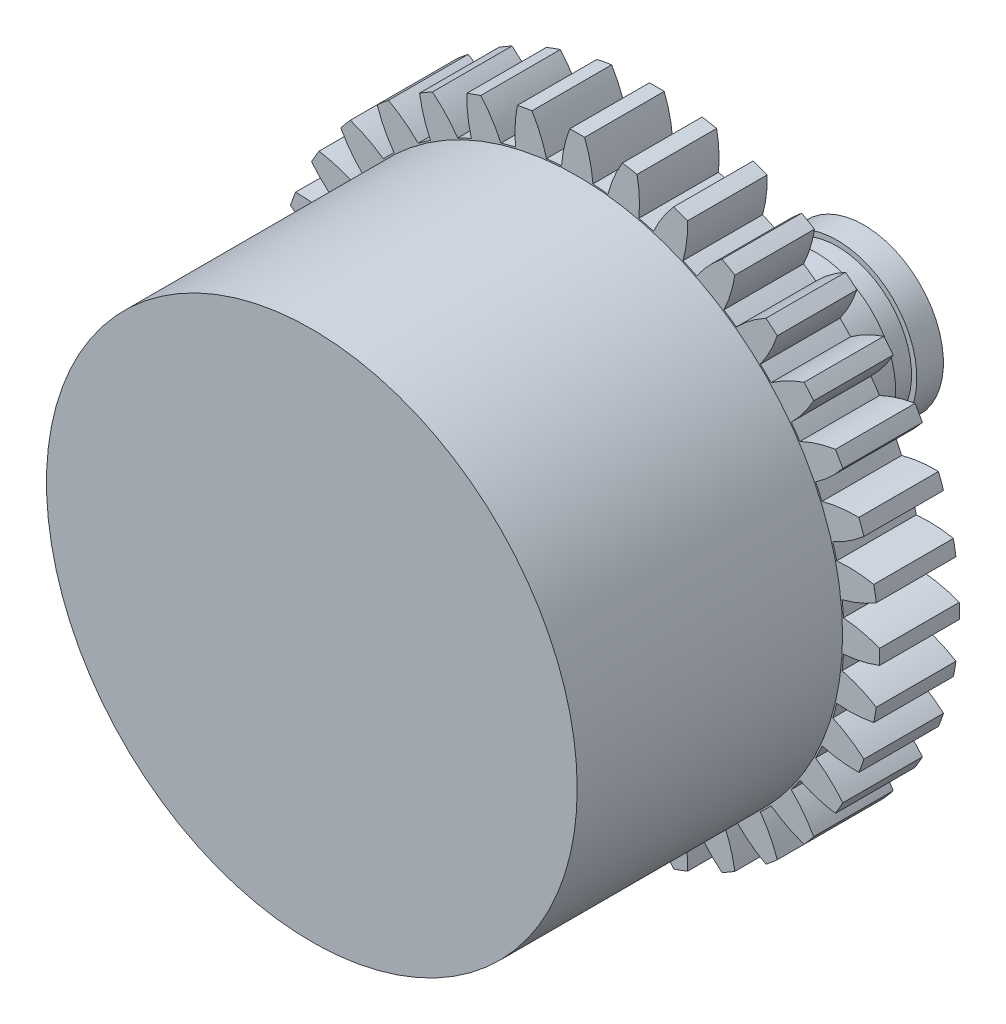
SolidWorks part; units mm, degrees
ref_plane "정면" through (0, 0, 0) normal (0, 0, 1) x (1, 0, 0)
ref_plane "윗면" through (0, 0, 0) normal (0, 1, 0) x (1, 0, 0)
ref_plane "우측면" through (0, 0, 0) normal (1, 0, 0) x (0, 0, -1)
sketch "스케치1" plane through (0, 0, 0) normal (0, 0, 1) x (1, 0, 0)
  circle A0 centre (0, 0) radius 5
  dimension "D1" = 10
extrude "보스-돌출1" add sketch "스케치1" along normal blind 5
sketch "스케치2" plane through (0, 0, 0) normal (0, 0, -1) x (-1, 0, 0)
  circle A0 centre (0, 0) radius 1.5
  dimension "D1" = 3
extrude "보스-돌출2" add sketch "스케치2" along normal blind 5.4
sketch "스케치3" plane through (0, 0, 0) normal (0, 0, -1) x (-1, 0, 0)
  circle A0 centre (0, 0) radius 2
  dimension "D1" = 4
extrude "보스-돌출3" add sketch "스케치3" along normal blind 2
sketch "스케치4" plane through (0, 0, -5.4) normal (0, 0, -1) x (-1, 0, 0)
  circle A0 centre (0, 0) radius 0.79
  dimension "D1" = 1.58
extrude "컷-돌출1" cut sketch "스케치4" against normal blind 1.5
sketch "스케치5" plane through (0, 0, 0) normal (0, 0, -1) x (-1, 0, 0)
  line L0 (0, 0) -> (0, 5.7) construction
  line L1 (0, 0) -> (-0.2355, 5.3949) construction
  line L2 (-0.2355, 5.3949) -> (-0.1399, 5.6983) construction
  line L3 (-0.2355, 5.3949) -> (-1.0666, 0.1696) construction
  circle A0 centre (0, 0) radius 5.4 construction
  circle A1 centre (0, 0) radius 5.7 construction
  circle A2 centre (0, 0) radius 5.025 construction
  circle A3 centre (0, 0) radius 1.08 construction
  arc A4 (-0.2958, 5.0163) -> (-0.1399, 5.6983) centre (2.074, 4.8335) cw
  arc A5 (0.2958, 5.0163) -> (0.1399, 5.6983) centre (-2.074, 4.8335) ccw
  arc A6 (-0.1399, 5.6983) -> (0.1399, 5.6983) centre (0, 0) cw
  arc A7 (1.1623, 4.8887) -> (1.1272, 5.5874) centre (-1.2031, 5.1202) ccw
  arc A8 (0.8517, 5.636) -> (1.1272, 5.5874) centre (0, 0) cw
  arc A9 (0.5798, 4.9914) -> (0.8517, 5.636) centre (2.8818, 4.3999) cw
  arc A10 (1.9936, 4.6126) -> (2.0804, 5.3068) centre (-0.2957, 5.2513) ccw
  arc A11 (1.8175, 5.4025) -> (2.0804, 5.3068) centre (0, 0) cw
  arc A12 (1.4378, 4.8149) -> (1.8175, 5.4025) centre (3.602, 3.8326) cw
  arc A13 (2.7643, 4.1964) -> (2.9703, 4.8649) centre (0.6206, 5.2229) ccw
  arc A14 (2.728, 5.0048) -> (2.9703, 4.8649) centre (0, 0) cw
  arc A15 (2.252, 4.4921) -> (2.728, 5.0048) centre (4.2128, 3.1489) cw
  arc A16 (3.451, 3.6526) -> (3.7699, 4.2752) centre (1.5181, 5.0358) ccw
  arc A17 (3.5556, 4.455) -> (3.7699, 4.2752) centre (0, 0) cw
  arc A18 (2.9978, 4.0328) -> (3.5556, 4.455) centre (4.6956, 2.3695) cw
  arc A19 (4.0328, 2.9978) -> (4.455, 3.5556) centre (2.3695, 4.6956) ccw
  arc A20 (4.2752, 3.7699) -> (4.455, 3.5556) centre (0, 0) cw
  arc A21 (3.6526, 3.451) -> (4.2752, 3.7699) centre (5.0358, 1.5181) cw
  arc A22 (4.4921, 2.252) -> (5.0048, 2.728) centre (3.1489, 4.2128) ccw
  arc A23 (4.8649, 2.9703) -> (5.0048, 2.728) centre (0, 0) cw
  arc A24 (4.1964, 2.7643) -> (4.8649, 2.9703) centre (5.2229, 0.6206) cw
  arc A25 (4.8149, 1.4378) -> (5.4025, 1.8175) centre (3.8326, 3.602) ccw
  arc A26 (5.3068, 2.0804) -> (5.4025, 1.8175) centre (0, 0) cw
  arc A27 (4.6126, 1.9936) -> (5.3068, 2.0804) centre (5.2513, -0.2957) cw
  arc A28 (4.9914, 0.5798) -> (5.636, 0.8517) centre (4.3999, 2.8818) ccw
  arc A29 (5.5874, 1.1272) -> (5.636, 0.8517) centre (0, 0) cw
  arc A30 (4.8887, 1.1623) -> (5.5874, 1.1272) centre (5.1202, -1.2031) cw
  arc A31 (5.0163, -0.2958) -> (5.6983, -0.1399) centre (4.8335, 2.074) ccw
  arc A32 (5.6983, 0.1399) -> (5.6983, -0.1399) centre (0, 0) cw
  arc A33 (5.0163, 0.2958) -> (5.6983, 0.1399) centre (4.8335, -2.074) cw
  arc A34 (4.8887, -1.1623) -> (5.5874, -1.1272) centre (5.1202, 1.2031) ccw
  arc A35 (5.636, -0.8517) -> (5.5874, -1.1272) centre (0, 0) cw
  arc A36 (4.9914, -0.5798) -> (5.636, -0.8517) centre (4.3999, -2.8818) cw
  arc A37 (4.6126, -1.9936) -> (5.3068, -2.0804) centre (5.2513, 0.2957) ccw
  arc A38 (5.4025, -1.8175) -> (5.3068, -2.0804) centre (0, 0) cw
  arc A39 (4.8149, -1.4378) -> (5.4025, -1.8175) centre (3.8326, -3.602) cw
  arc A40 (4.1964, -2.7643) -> (4.8649, -2.9703) centre (5.2229, -0.6206) ccw
  arc A41 (5.0048, -2.728) -> (4.8649, -2.9703) centre (0, 0) cw
  arc A42 (4.4921, -2.252) -> (5.0048, -2.728) centre (3.1489, -4.2128) cw
  arc A43 (3.6526, -3.451) -> (4.2752, -3.7699) centre (5.0358, -1.5181) ccw
  arc A44 (4.455, -3.5556) -> (4.2752, -3.7699) centre (0, 0) cw
  arc A45 (4.0328, -2.9978) -> (4.455, -3.5556) centre (2.3695, -4.6956) cw
  arc A46 (2.9978, -4.0328) -> (3.5556, -4.455) centre (4.6956, -2.3695) ccw
  arc A47 (3.7699, -4.2752) -> (3.5556, -4.455) centre (0, 0) cw
  arc A48 (3.451, -3.6526) -> (3.7699, -4.2752) centre (1.5181, -5.0358) cw
  arc A49 (2.252, -4.4921) -> (2.728, -5.0048) centre (4.2128, -3.1489) ccw
  arc A50 (2.9703, -4.8649) -> (2.728, -5.0048) centre (0, 0) cw
  arc A51 (2.7643, -4.1964) -> (2.9703, -4.8649) centre (0.6206, -5.2229) cw
  arc A52 (1.4378, -4.8149) -> (1.8175, -5.4025) centre (3.602, -3.8326) ccw
  arc A53 (2.0804, -5.3068) -> (1.8175, -5.4025) centre (0, 0) cw
  arc A54 (1.9936, -4.6126) -> (2.0804, -5.3068) centre (-0.2957, -5.2513) cw
  arc A55 (0.5798, -4.9914) -> (0.8517, -5.636) centre (2.8818, -4.3999) ccw
  arc A56 (1.1272, -5.5874) -> (0.8517, -5.636) centre (0, 0) cw
  arc A57 (1.1623, -4.8887) -> (1.1272, -5.5874) centre (-1.2031, -5.1202) cw
  arc A58 (-0.2958, -5.0163) -> (-0.1399, -5.6983) centre (2.074, -4.8335) ccw
  arc A59 (0.1399, -5.6983) -> (-0.1399, -5.6983) centre (0, 0) cw
  arc A60 (0.2958, -5.0163) -> (0.1399, -5.6983) centre (-2.074, -4.8335) cw
  arc A61 (-1.1623, -4.8887) -> (-1.1272, -5.5874) centre (1.2031, -5.1202) ccw
  arc A62 (-0.8517, -5.636) -> (-1.1272, -5.5874) centre (0, 0) cw
  arc A63 (-0.5798, -4.9914) -> (-0.8517, -5.636) centre (-2.8818, -4.3999) cw
  arc A64 (-1.9936, -4.6126) -> (-2.0804, -5.3068) centre (0.2957, -5.2513) ccw
  arc A65 (-1.8175, -5.4025) -> (-2.0804, -5.3068) centre (0, 0) cw
  arc A66 (-1.4378, -4.8149) -> (-1.8175, -5.4025) centre (-3.602, -3.8326) cw
  arc A67 (-2.7643, -4.1964) -> (-2.9703, -4.8649) centre (-0.6206, -5.2229) ccw
  arc A68 (-2.728, -5.0048) -> (-2.9703, -4.8649) centre (0, 0) cw
  arc A69 (-2.252, -4.4921) -> (-2.728, -5.0048) centre (-4.2128, -3.1489) cw
  arc A70 (-3.451, -3.6526) -> (-3.7699, -4.2752) centre (-1.5181, -5.0358) ccw
  arc A71 (-3.5556, -4.455) -> (-3.7699, -4.2752) centre (0, 0) cw
  arc A72 (-2.9978, -4.0328) -> (-3.5556, -4.455) centre (-4.6956, -2.3695) cw
  arc A73 (-4.0328, -2.9978) -> (-4.455, -3.5556) centre (-2.3695, -4.6956) ccw
  arc A74 (-4.2752, -3.7699) -> (-4.455, -3.5556) centre (0, 0) cw
  arc A75 (-3.6526, -3.451) -> (-4.2752, -3.7699) centre (-5.0358, -1.5181) cw
  arc A76 (-4.4921, -2.252) -> (-5.0048, -2.728) centre (-3.1489, -4.2128) ccw
  arc A77 (-4.8649, -2.9703) -> (-5.0048, -2.728) centre (0, 0) cw
  arc A78 (-4.1964, -2.7643) -> (-4.8649, -2.9703) centre (-5.2229, -0.6206) cw
  arc A79 (-4.8149, -1.4378) -> (-5.4025, -1.8175) centre (-3.8326, -3.602) ccw
  arc A80 (-5.3068, -2.0804) -> (-5.4025, -1.8175) centre (0, 0) cw
  arc A81 (-4.6126, -1.9936) -> (-5.3068, -2.0804) centre (-5.2513, 0.2957) cw
  arc A82 (-4.9914, -0.5798) -> (-5.636, -0.8517) centre (-4.3999, -2.8818) ccw
  arc A83 (-5.5874, -1.1272) -> (-5.636, -0.8517) centre (0, 0) cw
  arc A84 (-4.8887, -1.1623) -> (-5.5874, -1.1272) centre (-5.1202, 1.2031) cw
  arc A85 (-5.0163, 0.2958) -> (-5.6983, 0.1399) centre (-4.8335, -2.074) ccw
  arc A86 (-5.6983, -0.1399) -> (-5.6983, 0.1399) centre (0, 0) cw
  arc A87 (-5.0163, -0.2958) -> (-5.6983, -0.1399) centre (-4.8335, 2.074) cw
  arc A88 (-4.8887, 1.1623) -> (-5.5874, 1.1272) centre (-5.1202, -1.2031) ccw
  arc A89 (-5.636, 0.8517) -> (-5.5874, 1.1272) centre (0, 0) cw
  arc A90 (-4.9914, 0.5798) -> (-5.636, 0.8517) centre (-4.3999, 2.8818) cw
  arc A91 (-4.6126, 1.9936) -> (-5.3068, 2.0804) centre (-5.2513, -0.2957) ccw
  arc A92 (-5.4025, 1.8175) -> (-5.3068, 2.0804) centre (0, 0) cw
  arc A93 (-4.8149, 1.4378) -> (-5.4025, 1.8175) centre (-3.8326, 3.602) cw
  arc A94 (-4.1964, 2.7643) -> (-4.8649, 2.9703) centre (-5.2229, 0.6206) ccw
  arc A95 (-5.0048, 2.728) -> (-4.8649, 2.9703) centre (0, 0) cw
  arc A96 (-4.4921, 2.252) -> (-5.0048, 2.728) centre (-3.1489, 4.2128) cw
  arc A97 (-3.6526, 3.451) -> (-4.2752, 3.7699) centre (-5.0358, 1.5181) ccw
  arc A98 (-4.455, 3.5556) -> (-4.2752, 3.7699) centre (0, 0) cw
  arc A99 (-4.0328, 2.9978) -> (-4.455, 3.5556) centre (-2.3695, 4.6956) cw
  arc A100 (-2.9978, 4.0328) -> (-3.5556, 4.455) centre (-4.6956, 2.3695) ccw
  arc A101 (-3.7699, 4.2752) -> (-3.5556, 4.455) centre (0, 0) cw
  arc A102 (-3.451, 3.6526) -> (-3.7699, 4.2752) centre (-1.5181, 5.0358) cw
  arc A103 (-2.252, 4.4921) -> (-2.728, 5.0048) centre (-4.2128, 3.1489) ccw
  arc A104 (-2.9703, 4.8649) -> (-2.728, 5.0048) centre (0, 0) cw
  arc A105 (-2.7643, 4.1964) -> (-2.9703, 4.8649) centre (-0.6206, 5.2229) cw
  arc A106 (-1.4378, 4.8149) -> (-1.8175, 5.4025) centre (-3.602, 3.8326) ccw
  arc A107 (-2.0804, 5.3068) -> (-1.8175, 5.4025) centre (0, 0) cw
  arc A108 (-1.9936, 4.6126) -> (-2.0804, 5.3068) centre (0.2957, 5.2513) cw
  arc A109 (-0.5798, 4.9914) -> (-0.8517, 5.636) centre (-2.8818, 4.3999) ccw
  arc A110 (-1.1272, 5.5874) -> (-0.8517, 5.636) centre (0, 0) cw
  arc A111 (-1.1623, 4.8887) -> (-1.1272, 5.5874) centre (1.2031, 5.1202) cw
  arc A112 (0.2958, 5.0163) -> (0.5798, 4.9914) centre (0, 0) cw
  arc A113 (1.1623, 4.8887) -> (1.4378, 4.8149) centre (0, 0) cw
  arc A114 (1.9936, 4.6126) -> (2.252, 4.4921) centre (0, 0) cw
  arc A115 (2.7643, 4.1964) -> (2.9978, 4.0328) centre (0, 0) cw
  arc A116 (3.451, 3.6526) -> (3.6526, 3.451) centre (0, 0) cw
  arc A117 (4.0328, 2.9978) -> (4.1964, 2.7643) centre (0, 0) cw
  arc A118 (4.4921, 2.252) -> (4.6126, 1.9936) centre (0, 0) cw
  arc A119 (4.8149, 1.4378) -> (4.8887, 1.1623) centre (0, 0) cw
  arc A120 (4.9914, 0.5798) -> (5.0163, 0.2958) centre (0, 0) cw
  arc A121 (5.0163, -0.2958) -> (4.9914, -0.5798) centre (0, 0) cw
  arc A122 (4.8887, -1.1623) -> (4.8149, -1.4378) centre (0, 0) cw
  arc A123 (4.6126, -1.9936) -> (4.4921, -2.252) centre (0, 0) cw
  arc A124 (4.1964, -2.7643) -> (4.0328, -2.9978) centre (0, 0) cw
  arc A125 (3.6526, -3.451) -> (3.451, -3.6526) centre (0, 0) cw
  arc A126 (2.9978, -4.0328) -> (2.7643, -4.1964) centre (0, 0) cw
  arc A127 (2.252, -4.4921) -> (1.9936, -4.6126) centre (0, 0) cw
  arc A128 (1.4378, -4.8149) -> (1.1623, -4.8887) centre (0, 0) cw
  arc A129 (0.5798, -4.9914) -> (0.2958, -5.0163) centre (0, 0) cw
  arc A130 (-0.2958, -5.0163) -> (-0.5798, -4.9914) centre (0, 0) cw
  arc A131 (-1.1623, -4.8887) -> (-1.4378, -4.8149) centre (0, 0) cw
  arc A132 (-1.9936, -4.6126) -> (-2.252, -4.4921) centre (0, 0) cw
  arc A133 (-2.7643, -4.1964) -> (-2.9978, -4.0328) centre (0, 0) cw
  arc A134 (-3.451, -3.6526) -> (-3.6526, -3.451) centre (0, 0) cw
  arc A135 (-4.0328, -2.9978) -> (-4.1964, -2.7643) centre (0, 0) cw
  arc A136 (-4.4921, -2.252) -> (-4.6126, -1.9936) centre (0, 0) cw
  arc A137 (-4.8149, -1.4378) -> (-4.8887, -1.1623) centre (0, 0) cw
  arc A138 (-4.9914, -0.5798) -> (-5.0163, -0.2958) centre (0, 0) cw
  arc A139 (-5.0163, 0.2958) -> (-4.9914, 0.5798) centre (0, 0) cw
  arc A140 (-4.8887, 1.1623) -> (-4.8149, 1.4378) centre (0, 0) cw
  arc A141 (-4.6126, 1.9936) -> (-4.4921, 2.252) centre (0, 0) cw
  arc A142 (-4.1964, 2.7643) -> (-4.0328, 2.9978) centre (0, 0) cw
  arc A143 (-3.6526, 3.451) -> (-3.451, 3.6526) centre (0, 0) cw
  arc A144 (-2.9978, 4.0328) -> (-2.7643, 4.1964) centre (0, 0) cw
  arc A145 (-2.252, 4.4921) -> (-1.9936, 4.6126) centre (0, 0) cw
  arc A146 (-1.4378, 4.8149) -> (-1.1623, 4.8887) centre (0, 0) cw
  arc A147 (-0.5798, 4.9914) -> (-0.2958, 5.0163) centre (0, 0) cw
  point P12 (-0.2958, 5.0163)
  point P230 (0, 0)
  point P302 (0, 0)
  dimension "D1" = 10.8
  dimension "D2" = 0.375
  dimension "D3" = 0.3
  dimension "D6" = 2.16
  dimension "D4" = 2.5
  dimension "D5" = 20
  dimension "D7" = 36
  dimension "D8" = 36
extrude "보스-돌출4" add sketch "스케치5" along normal blind 1.5
sketch "스케치7" plane through (0, 0, -1.5) normal (0, 0, -1) x (-1, 0, 0)
  circle A0 centre (0, 0) radius 1.4
  circle A1 centre (0, 0) radius 2
  dimension "D1" = 4
  dimension "D2" = 2.8
extrude "컷-돌출3" cut sketch "스케치7" along normal blind 0.4 from offset 3
